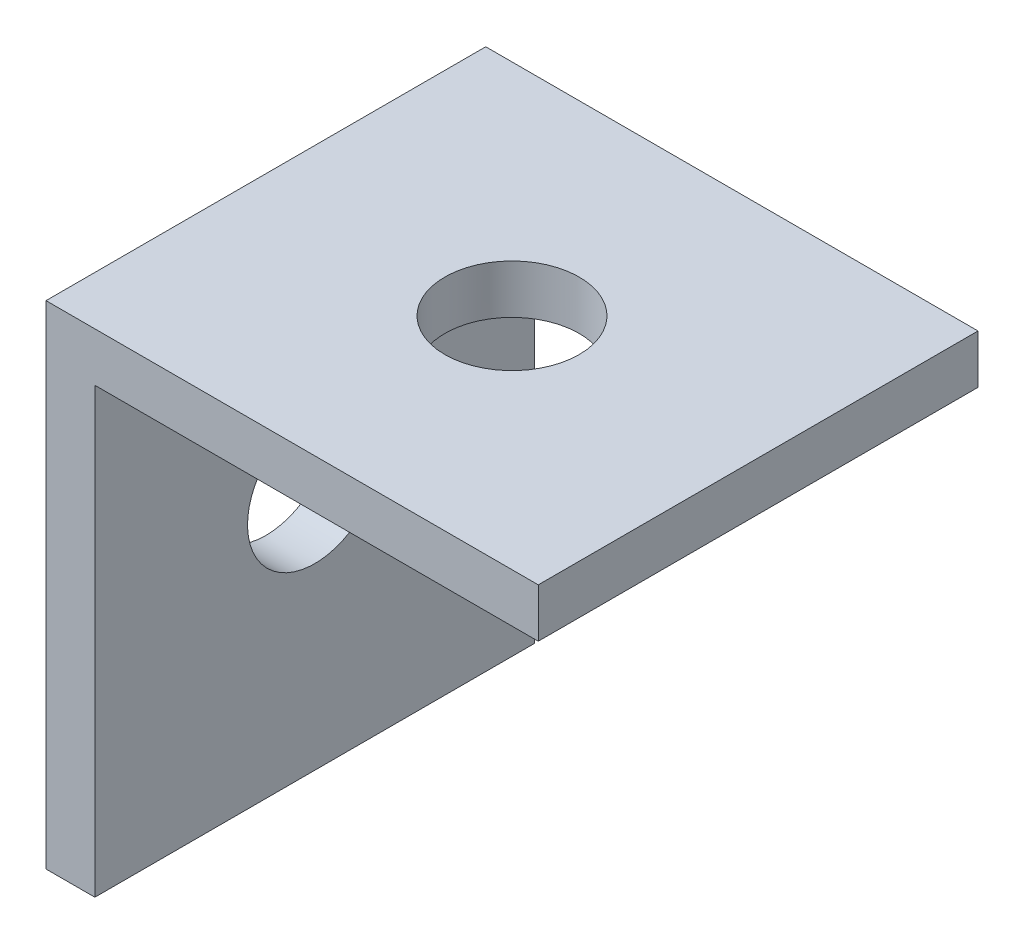
SolidWorks part; units mm, degrees
ref_plane "Front Plane" through (0, 0, 0) normal (0, 0, 1) x (1, 0, 0)
ref_plane "Top Plane" through (0, 0, 0) normal (0, 1, 0) x (1, 0, 0)
ref_plane "Right Plane" through (0, 0, 0) normal (1, 0, 0) x (0, 0, -1)
sketch "Sketch1" plane through (0, 0, 0) normal (0, 0, 1) x (1, 0, 0)
  line L0 (0, 0) -> (0, -20.15)
  line L1 (0, 0) -> (20.15, 0)
  line L2 (2, -2) -> (0, 0) construction
  line L3 (2, -2) -> (2, -20.15)
  line L4 (2, -20.15) -> (0, -20.15)
  line L5 (2, -2) -> (20.15, -2)
  line L6 (20.15, -2) -> (20.15, 0)
  dimension "D1" = 20.15
  dimension "D2" = 20.15
  dimension "D3" = 45
  dimension "D4" = 2
extrude "Boss-Extrude1" add sketch "Sketch1" against normal blind 18
sketch "Sketch2" plane through (0, -2, 0) normal (0, -1, 0) x (1, 0, 0)
  line L0 (10.075, 0) -> (10.075, -18) construction
  line L1 (0, 0) -> (20.15, 0) construction
  line L2 (0, 0) -> (0, -18) construction
  line L3 (0, -18) -> (20.15, -18) construction
  line L4 (20.15, 0) -> (20.15, -18) construction
  circle A0 centre (10.075, -9) radius 2.75
  dimension "D1" = 5.5
extrude "Cut-Extrude1" cut sketch "Sketch2" against normal blind 18
sketch "Sketch3" plane through (2, 0, 0) normal (1, 0, 0) x (0, 0, -1)
  line L0 (0, -10.075) -> (18, -10.075) construction
  line L1 (0, 0) -> (18, 0) construction
  line L2 (0, 0) -> (0, -20.15) construction
  line L3 (0, -20.15) -> (18, -20.15) construction
  line L4 (18, 0) -> (18, -20.15) construction
  circle A0 centre (9, -10.075) radius 2.75
  dimension "D1" = 5.5
extrude "Cut-Extrude2" cut sketch "Sketch3" against normal blind 18
